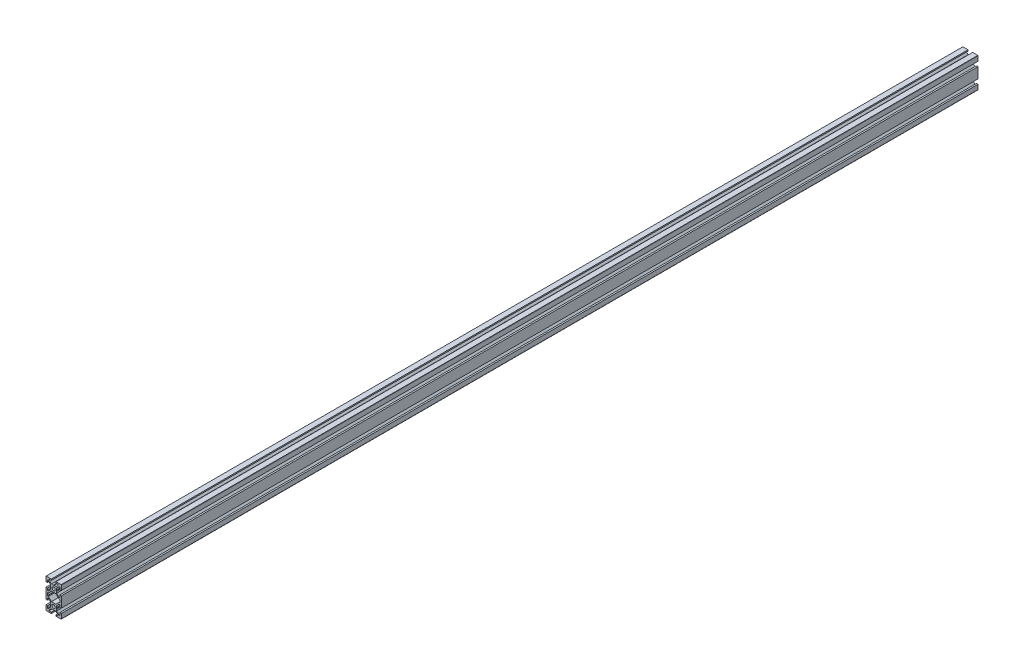
SolidWorks part; units mm, degrees
material "6063-T5"
ref_plane "Front Plane" through (0, 0, 0) normal (0, 0, 1) x (1, 0, 0)
ref_plane "Top Plane" through (0, 0, 0) normal (0, 1, 0) x (1, 0, 0)
ref_plane "Right Plane" through (0, 0, 0) normal (1, 0, 0) x (0, 0, -1)
ref_plane "Plane1" through (0, 0, -1000) normal (0, 0, -1) x (-1, 0, 0)
sketch "Sketch1" plane through (0, 0, -1000) normal (0, 0, -1) x (-1, 0, 0)
  line L0 (10, -7) -> (10, 7)
  line L1 (10, 7) -> (8, 7)
  line L2 (8, 7) -> (8, 4)
  line L3 (8, 4) -> (7.0607, 4)
  line L4 (7.0607, 4) -> (4, 7.0607)
  line L5 (4, 7.0607) -> (4, 9.4804)
  line L6 (4, 9.4804) -> (3.7, 10)
  line L7 (3.7, 10) -> (4, 10.5196)
  line L8 (4, 10.5196) -> (4, 12.9393)
  line L9 (4, 12.9393) -> (7.0607, 16)
  line L10 (7.0607, 16) -> (8, 16)
  line L11 (8, 16) -> (8, 13)
  line L12 (8, 13) -> (10, 13)
  line L13 (10, 13) -> (10, 19)
  line L14 (9.8, 19.6) -> (3, 19.6)
  line L15 (3, 19.6) -> (3, 18)
  line L16 (3, 18) -> (6, 18)
  line L17 (6, 18) -> (6, 17.0607)
  line L18 (6, 17.0607) -> (2.9393, 14)
  line L19 (2.9393, 14) -> (0.5196, 14)
  line L20 (0.5196, 14) -> (0, 13.7)
  line L21 (0, 13.7) -> (-0.5196, 14)
  line L22 (-0.5196, 14) -> (-2.9393, 14)
  line L23 (-2.9393, 14) -> (-6, 17.0607)
  line L24 (-6, 17.0607) -> (-6, 18)
  line L25 (-6, 18) -> (-3, 18)
  line L26 (-3, 18) -> (-3, 19.6)
  line L27 (-3, 19.6) -> (-9.8, 19.6)
  line L28 (-10, 19) -> (-10, 13)
  line L29 (-10, 13) -> (-8, 13)
  line L30 (-8, 13) -> (-8, 16)
  line L31 (-8, 16) -> (-7.0607, 16)
  line L32 (-7.0607, 16) -> (-4, 12.9393)
  line L33 (-4, 12.9393) -> (-4, 10.5196)
  line L34 (-4, 10.5196) -> (-3.7, 10)
  line L35 (-3.7, 10) -> (-4, 9.4804)
  line L36 (-4, 9.4804) -> (-4, 7.0607)
  line L37 (-4, 7.0607) -> (-7.0607, 4)
  line L38 (-7.0607, 4) -> (-8, 4)
  line L39 (-8, 4) -> (-8, 7)
  line L40 (-8, 7) -> (-10, 7)
  line L41 (-10, 7) -> (-10, -7)
  line L42 (-10, -7) -> (-8, -7)
  line L43 (-8, -7) -> (-8, -4)
  line L44 (-8, -4) -> (-7.0607, -4)
  line L45 (-7.0607, -4) -> (-4, -7.0607)
  line L46 (-4, -7.0607) -> (-4, -9.4804)
  line L47 (-4, -9.4804) -> (-3.7, -10)
  line L48 (-3.7, -10) -> (-4, -10.5196)
  line L49 (-4, -10.5196) -> (-4, -12.9393)
  line L50 (-4, -12.9393) -> (-7.0607, -16)
  line L51 (-7.0607, -16) -> (-8, -16)
  line L52 (-8, -16) -> (-8, -13)
  line L53 (-8, -13) -> (-10, -13)
  line L54 (-10, -13) -> (-10, -19)
  line L55 (-9.8, -19.6) -> (-3, -19.6)
  line L56 (-3, -19.6) -> (-3, -18)
  line L57 (-3, -18) -> (-6, -18)
  line L58 (-6, -18) -> (-6, -17.0607)
  line L59 (-6, -17.0607) -> (-2.9393, -14)
  line L60 (-2.9393, -14) -> (-0.5196, -14)
  line L61 (-0.5196, -14) -> (0, -13.7)
  line L62 (0, -13.7) -> (0.5196, -14)
  line L63 (0.5196, -14) -> (2.9393, -14)
  line L64 (2.9393, -14) -> (6, -17.0607)
  line L65 (6, -17.0607) -> (6, -18)
  line L66 (6, -18) -> (3, -18)
  line L67 (3, -18) -> (3, -19.6)
  line L68 (3, -19.6) -> (9.8, -19.6)
  line L69 (10, -19) -> (10, -13)
  line L70 (10, -13) -> (8, -13)
  line L71 (8, -13) -> (8, -16)
  line L72 (8, -16) -> (7.0607, -16)
  line L73 (7.0607, -16) -> (4, -12.9393)
  line L74 (4, -12.9393) -> (4, -10.5196)
  line L75 (4, -10.5196) -> (3.7, -10)
  line L76 (3.7, -10) -> (4, -9.4804)
  line L77 (4, -9.4804) -> (4, -7.0607)
  line L78 (4, -7.0607) -> (7.0607, -4)
  line L79 (7.0607, -4) -> (8, -4)
  line L80 (8, -4) -> (8, -7)
  line L81 (8, -7) -> (10, -7)
  line L82 (8, 1.7) -> (8, -1.7)
  line L83 (7.7, -2) -> (7.0636, -2)
  line L84 (6.8515, -2.0879) -> (2.9393, -6)
  line L85 (2.9393, -6) -> (-2.9393, -6)
  line L86 (-2.9393, -6) -> (-6.8515, -2.0879)
  line L87 (-7.0636, -2) -> (-7.7, -2)
  line L88 (-8, -1.7) -> (-8, 1.7)
  line L89 (-7.7, 2) -> (-7.0636, 2)
  line L90 (-6.8515, 2.0879) -> (-2.9393, 6)
  line L91 (-2.9393, 6) -> (2.9393, 6)
  line L92 (2.9393, 6) -> (6.8515, 2.0879)
  line L93 (7.0636, 2) -> (7.7, 2)
  arc A0 (10, 19) -> (9.8, 19.6) centre (9, 19) ccw
  arc A1 (-9.8, 19.6) -> (-10, 19) centre (-9, 19) ccw
  arc A2 (-10, -19) -> (-9.8, -19.6) centre (-9, -19) ccw
  arc A3 (9.8, -19.6) -> (10, -19) centre (9, -19) ccw
  arc A4 (7.7, 2) -> (8, 1.7) centre (7.7, 1.7) cw
  arc A5 (8, -1.7) -> (7.7, -2) centre (7.7, -1.7) cw
  arc A6 (7.0636, -2) -> (6.8515, -2.0879) centre (7.0636, -2.3) ccw
  arc A7 (-6.8515, -2.0879) -> (-7.0636, -2) centre (-7.0636, -2.3) ccw
  arc A8 (-7.7, -2) -> (-8, -1.7) centre (-7.7, -1.7) cw
  arc A9 (-8, 1.7) -> (-7.7, 2) centre (-7.7, 1.7) cw
  arc A10 (-7.0636, 2) -> (-6.8515, 2.0879) centre (-7.0636, 2.3) ccw
  arc A11 (6.8515, 2.0879) -> (7.0636, 2) centre (7.0636, 2.3) ccw
  circle A12 centre (0, -10) radius 2.1
  circle A13 centre (0, 10) radius 2.1
extrude "Boss-Extrude1" add sketch "Sketch1" against normal blind 1200
